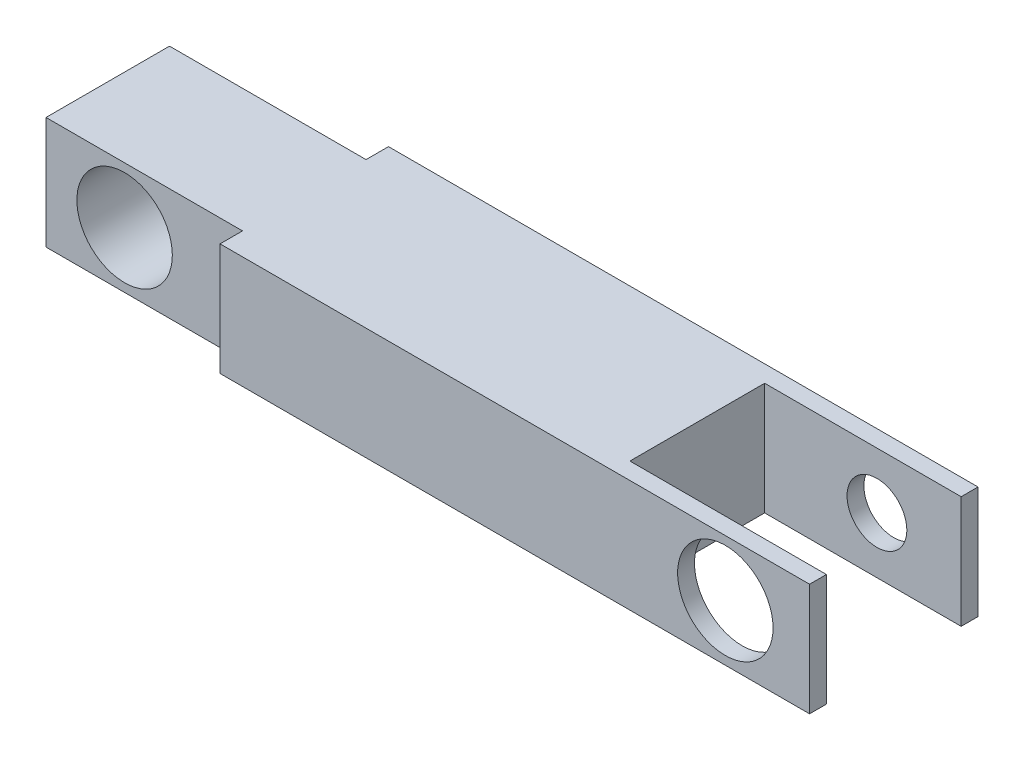
SolidWorks part; units mm, degrees
ref_plane "Front Plane" through (0, 0, 0) normal (0, 0, 1) x (1, 0, 0)
ref_plane "Top Plane" through (0, 0, 0) normal (0, 1, 0) x (1, 0, 0)
ref_plane "Right Plane" through (0, 0, 0) normal (1, 0, 0) x (0, 0, -1)
sketch "Sketch2" plane through (0, 0, 0) normal (0, 0, 1) x (1, 0, 0)
  line L0 (-72.5199, -2.2752) -> (-72.5199, -7.3552)
  line L1 (-72.5199, -7.3552) -> (-36.9599, -7.3552)
  line L2 (-36.9599, -7.3552) -> (-36.9599, -2.2752)
  line L3 (-36.9599, -2.2752) -> (-72.5199, -2.2752)
  dimension "D1" = 35.56
  dimension "D2" = 5.08
extrude "Boss-Extrude1" add sketch "Sketch2" along normal blind 7.62
sketch "Sketch6" plane through (0, 0, 7.62) normal (0, 0, 1) x (1, 0, 0)
  line L0 (-36.9599, -7.3552) -> (-36.9599, -2.2752) construction
  point P0 (-68.9639, -4.8152)
  point P1 (-40.7699, -4.8152)
  point P4 (0, 0)
  point P5 (0, 0)
  point P6 (0, 0)
  point P7 (0, 0)
  dimension "D2" = 3.81
  dimension "D3" = 28.194
sketch "Sketch7" plane through (0, -7.3552, 0) normal (0, -1, 0) x (1, 0, 0)
  line L0 (-36.9599, 0.762) -> (-45.8499, 0.762)
  line L1 (-36.9599, 7.62) -> (-36.9599, 0) construction
  line L2 (-45.8499, 0.762) -> (-45.8499, 6.858)
  line L3 (-45.8499, 6.858) -> (-36.9599, 6.858)
  line L4 (-36.9599, 6.858) -> (-36.9599, 0.762)
  line L5 (-72.5199, 0) -> (-36.9599, 0) construction
  line L6 (-72.5199, 7.62) -> (-36.9599, 7.62) construction
  line L7 (-72.5199, 0) -> (-63.6299, 0)
  line L8 (-63.6299, 0) -> (-63.6299, 1.016)
  line L9 (-63.6299, 1.016) -> (-72.5199, 1.016)
  line L10 (-72.5199, 7.62) -> (-72.5199, 0) construction
  line L11 (-72.5199, 1.016) -> (-72.5199, 6.604)
  line L12 (-72.5199, 6.604) -> (-63.6299, 6.604)
  line L13 (-63.6299, 6.604) -> (-63.6299, 7.62)
  line L14 (-63.6299, 7.62) -> (-72.5199, 7.62)
  line L15 (-72.5199, 7.62) -> (-72.5199, 0)
  line M7 (-72.5199, 0) -> (-36.9599, 0)
  line M8 (-36.9599, 0) -> (-36.9599, 7.62)
  line M9 (-36.9599, 7.62) -> (-72.5199, 7.62)
  line M10 (-72.5199, 7.62) -> (-72.5199, 0)
  dimension "D1" = 8.89
  dimension "D2" = 0.762
  dimension "D3" = 0.762
  dimension "D4" = 1.016
  dimension "D5" = 1.016
  dimension "D6" = 8.89
  dimension "D7" = 8.89
extrude "Cut-Extrude2" cut sketch "Sketch7" against normal through all contours L3 L2 L0 M8 | L8 L9 M10 M7 | L12 L13 M9 M10
sketch "Sketch8" plane through (0, 0, 7.62) normal (0, 0, 1) x (1, 0, 0)
  circle A0 centre (-40.7699, -4.8152) radius 2.159
  dimension "D1" = 4.318
extrude "Cut-Extrude3" cut sketch "Sketch8" against normal up to next
sketch "Sketch9" plane through (0, 0, 6.604) normal (0, 0, 1) x (1, 0, 0)
  circle A0 centre (-68.9639, -4.8152) radius 2.159
  dimension "D1" = 4.318
extrude "Cut-Extrude4" cut sketch "Sketch9" against normal through all
hole_wizard "#6-32 Tapped Hole1" positions "Sketch11" profile "Sketch12" tap size "#6-32" standard "ANSI Inch" end condition up to next
sketch "Sketch11" plane through (0, 0, 0) normal (0, 0, -1) x (-1, 0, 0)
  point P0 (40.7699, -4.8152)
sketch "Sketch12" plane through (-40.7699, -4.8152, 0) normal (1, 0, 0) x (0, 1, 0)
  line L0 (0, 0) -> (0, 0.762)
  line L1 (0, 0.762) -> (1.3525, 0.762)
  line L2 (1.3525, 0.762) -> (1.3525, 0)
  line L5 (1.3525, 0) -> (0, 0)
  line L11 (0, -6.35) -> (0, 107.95) construction
  dimension "Thread Major Dia." = 2.7051
  dimension "Thru Tap Drill Depth" = 0.762
ref_plane "Plane1" through (0, -4.8152, 0) normal (0, 1, 0) x (1, 0, 0)
ref_plane "Plane2" through (0, 0, 3.81) normal (0, 0, -1) x (-1, 0, 0)
